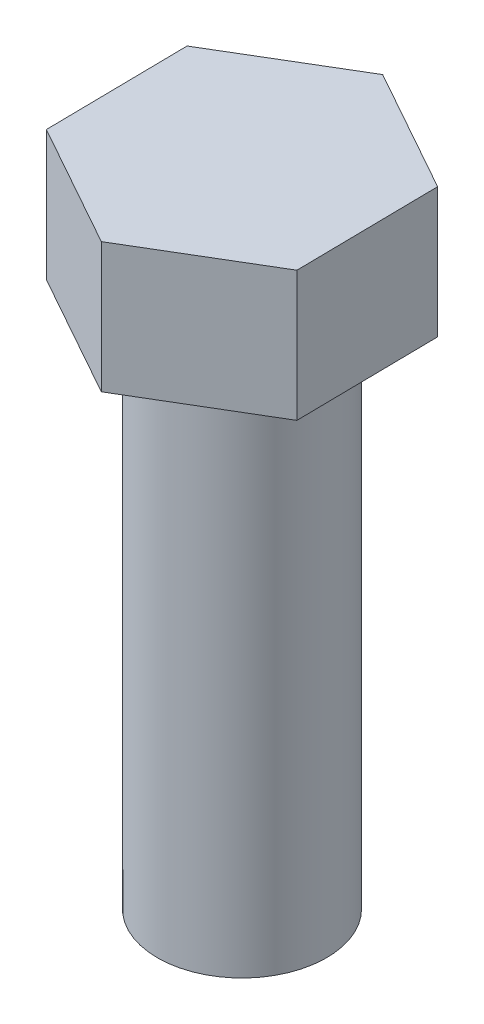
SolidWorks part; units mm, degrees
ref_plane "Front" through (0, 0, 0) normal (0, 0, 1) x (1, 0, 0)
ref_plane "Top" through (0, 0, 0) normal (0, 1, 0) x (1, 0, 0)
ref_plane "Right" through (0, 0, 0) normal (1, 0, 0) x (0, 0, -1)
sketch "Эскиз2" plane through (0, 0, 0) normal (0, 1, 0) x (1, 0, 0)
  circle A0 centre (0, 0) radius 6.5
extrude "Бобышка-Вытянуть1" add sketch "Эскиз2" along normal blind 40
sketch "Эскиз3" plane through (0, 40, 0) normal (0, 1, 0) x (1, 0, 0)
  line L1 (-9.5755, 5.3518) -> (-9.4226, -5.6167)
  line L2 (-9.4226, -5.6167) -> (0.1529, -10.9686)
  line L3 (0.1529, -10.9686) -> (9.5755, -5.3518)
  line L4 (9.5755, -5.3518) -> (9.4226, 5.6167)
  line L5 (9.4226, 5.6167) -> (-0.1529, 10.9686)
  line L6 (-0.1529, 10.9686) -> (-9.5755, 5.3518)
  circle A0 centre (0, 0) radius 9.5 construction
extrude "Бобышка-Вытянуть2" add sketch "Эскиз3" along normal blind 10
